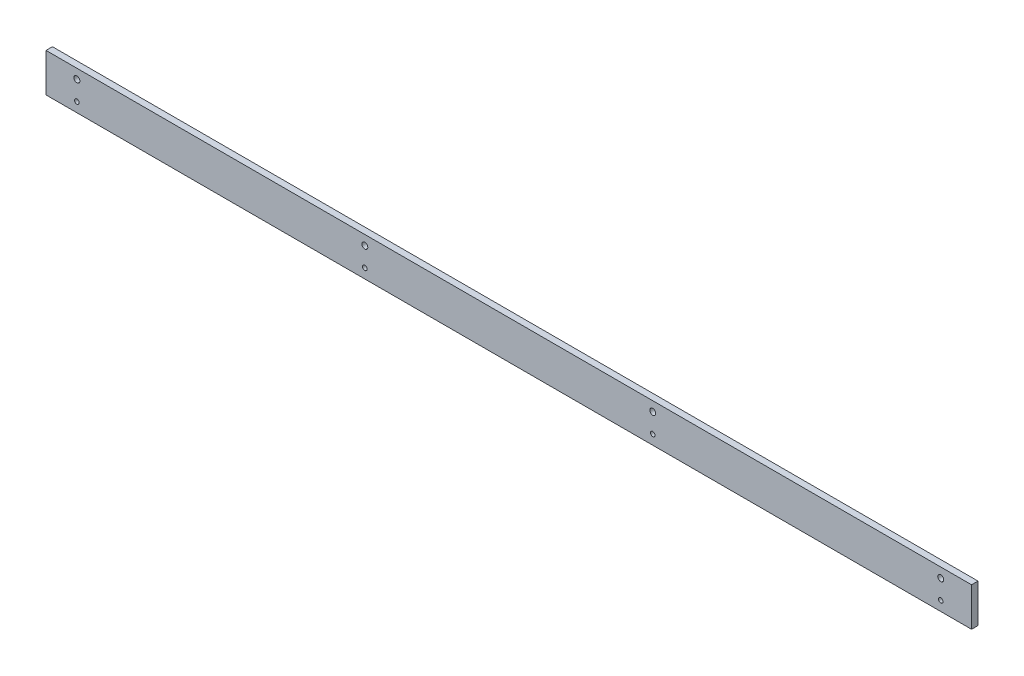
SolidWorks part; units mm, degrees
ref_plane "Front Plane" through (0, 0, 0) normal (0, 0, 1) x (1, 0, 0)
ref_plane "Top Plane" through (0, 0, 0) normal (0, 1, 0) x (1, 0, 0)
ref_plane "Right Plane" through (0, 0, 0) normal (1, 0, 0) x (0, 0, -1)
sketch "Sketch1" plane through (0, 0, 0) normal (0, 0, 1) x (1, 0, 0)
  line L1 (228.6, 9.525) -> (-228.6, 9.525)
  line L2 (228.6, 9.525) -> (228.6, -9.525)
  line L3 (228.6, -9.525) -> (-228.6, -9.525)
  line L4 (-228.6, 9.525) -> (-228.6, -9.525)
  line L5 (0, -9.525) -> (0, 9.525) construction
  line L6 (228.6, 0) -> (-228.6, 0) construction
  point P0 (0, 0)
  dimension "D1" = 457.2
  dimension "D2" = 19.05
extrude "Boss-Extrude1" add sketch "Sketch1" along normal blind 3.175
sketch "Sketch2" plane through (0, 0, 3.175) normal (0, 0, 1) x (1, 0, 0)
  line L1 (213.36, 4.7625) -> (-213.36, 4.7625) construction
  line L2 (213.36, 4.7625) -> (213.36, -4.7625) construction
  line L3 (213.36, -4.7625) -> (-213.36, -4.7625) construction
  line L4 (-213.36, 4.7625) -> (-213.36, -4.7625) construction
  line L5 (0, -4.7625) -> (0, 4.7625) construction
  line L6 (213.36, 0) -> (-213.36, 0) construction
  point P0 (0, 0)
  point P4 (-71.12, 4.7625)
  point P5 (-71.12, -4.7625)
  point P6 (71.12, -4.7625)
  point P7 (71.12, 4.7625)
  point P8 (0, 0)
  point P9 (0, 0)
  dimension "D1" = 426.72
  dimension "D2" = 71.12
  dimension "D3" = 71.12
  dimension "D4" = 142.24
  dimension "D5" = 142.24
  dimension "D6" = 9.525
hole_wizard "#4 Clearance Hole1" positions "Sketch3" profile "Sketch4" hole size "#4" standard "ANSI Inch" end condition through all
sketch "Sketch3" plane through (0, 0, 3.175) normal (0, 0, 1) x (1, 0, 0)
  point P0 (-213.36, 4.7625)
  point P6 (-71.12, 4.7625)
  point P9 (71.12, 4.7625)
  point P12 (213.36, 4.7625)
  point P16 (0, 0)
sketch "Sketch4" plane through (-213.36, 4.7625, 3.175) normal (1, 0, 0) x (0, -1, 0)
  line L0 (0, 0) -> (0, 3.175)
  line L1 (0, 3.175) -> (1.4732, 3.175)
  line L2 (1.4732, 3.175) -> (1.4732, 0)
  line L5 (1.4732, 0) -> (0, 0)
  line L11 (0, -6.35) -> (0, 107.95) construction
  dimension "Thru Hole Dia." = 2.9464
  dimension "Thru Hole Depth" = 3.175
hole_wizard "#4-40 Tapped Hole1" positions "Sketch5" profile "Sketch6" tap size "#4-40" standard "ANSI Inch" end condition through all
sketch "Sketch5" plane through (0, 0, 3.175) normal (0, 0, 1) x (1, 0, 0)
  point P0 (-213.36, -4.7625)
  point P3 (-71.12, -4.7625)
  point P6 (71.12, -4.7625)
  point P9 (213.36, -4.7625)
sketch "Sketch6" plane through (-213.36, -4.7625, 3.175) normal (1, 0, 0) x (0, -1, 0)
  line L0 (0, 0) -> (0, 3.175)
  line L1 (0, 3.175) -> (1.1303, 3.175)
  line L2 (1.1303, 3.175) -> (1.1303, 0)
  line L5 (1.1303, 0) -> (0, 0)
  line L11 (0, -6.35) -> (0, 107.95) construction
  dimension "Thru Tap Drill Dia." = 2.2606
  dimension "Thru Tap Drill Depth" = 3.175
cosmetic thread "Hole Thread1" parameters "D2"=2.8448
cosmetic thread "Hole Thread2" parameters "D2"=2.8448
cosmetic thread "Hole Thread3" parameters "D2"=2.8448
cosmetic thread "Hole Thread4" parameters "D2"=2.8448
